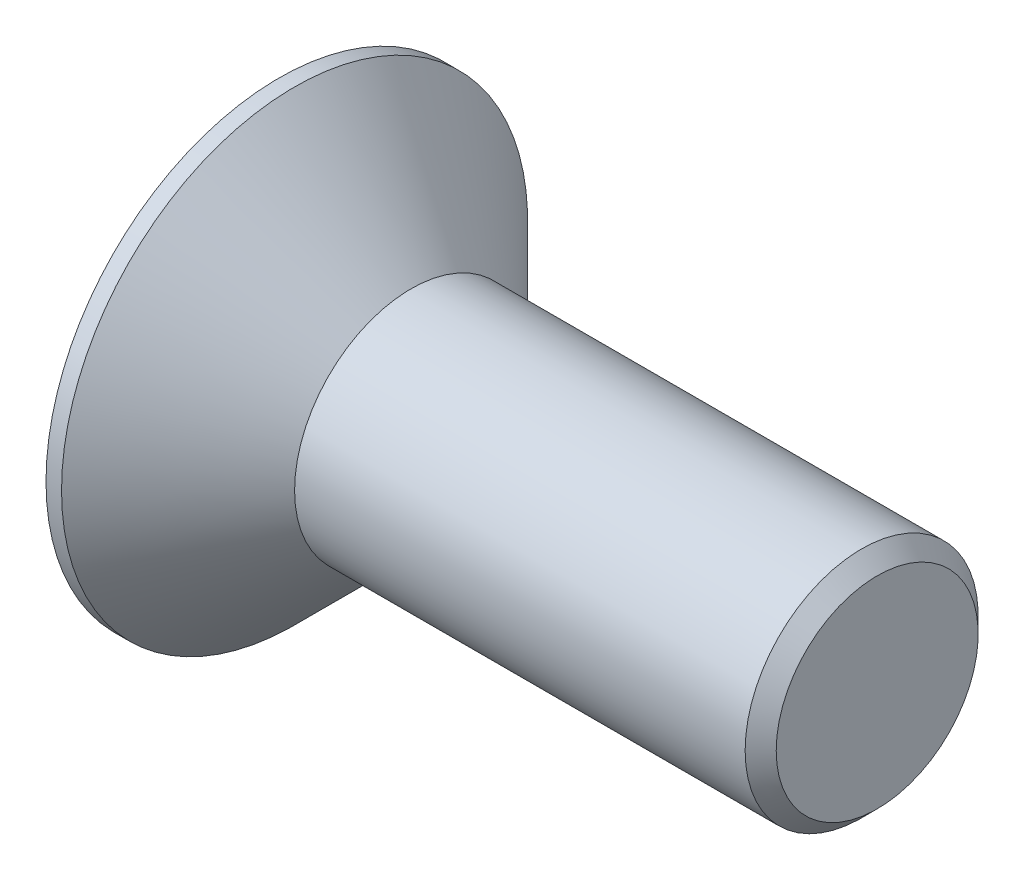
SolidWorks part; units mm, degrees
ref_plane "Front" through (0, 0, 0) normal (0, 0, 1) x (1, 0, 0)
ref_plane "Top" through (0, 0, 0) normal (0, 1, 0) x (1, 0, 0)
ref_plane "Right" through (0, 0, 0) normal (1, 0, 0) x (0, 0, -1)
sketch "Esquisse1" plane through (0, 0, 0) normal (0, 0, 1) x (1, 0, 0)
  line L0 (0, 0) -> (7.7, 0) construction
  line L1 (0, 0) -> (0, 3)
  line L2 (0, 3) -> (0.2, 3)
  line L3 (0.2, 3) -> (1.7, 1.5)
  line L4 (1.7, 1.5) -> (7.7, 1.5)
  line L5 (7.7, 1.5) -> (7.7, 0)
  line L6 (0, 0) -> (7.7, 0)
  dimension "D1" = 45
  dimension "D2" = 0.2
  dimension "D3" = 6
  dimension "D4" = 3
  dimension "D5" = 6
revolve "Révolution1" add sketch "Esquisse1" angle 360 about L0
sketch "Esquisse2" plane through (0, 0, 0) normal (-1, 0, 0) x (0, 0, 1)
  line L1 (0.433, -0.75) -> (0.866, 0)
  line L2 (0.866, 0) -> (0.433, 0.75)
  line L3 (0.433, 0.75) -> (-0.433, 0.75)
  line L4 (-0.433, 0.75) -> (-0.866, 0)
  line L5 (-0.866, 0) -> (-0.433, -0.75)
  line L6 (-0.433, -0.75) -> (0.433, -0.75)
  circle A0 centre (0, 0) radius 0.75 construction
  dimension "D1" = 1.5
extrude "Enlèv. mat.-Extru.1" cut sketch "Esquisse2" against normal blind 2
chamfer "Chanfrein1" distance 0.2 angle 45 1 edges at (7.7, 0, 1.5)
